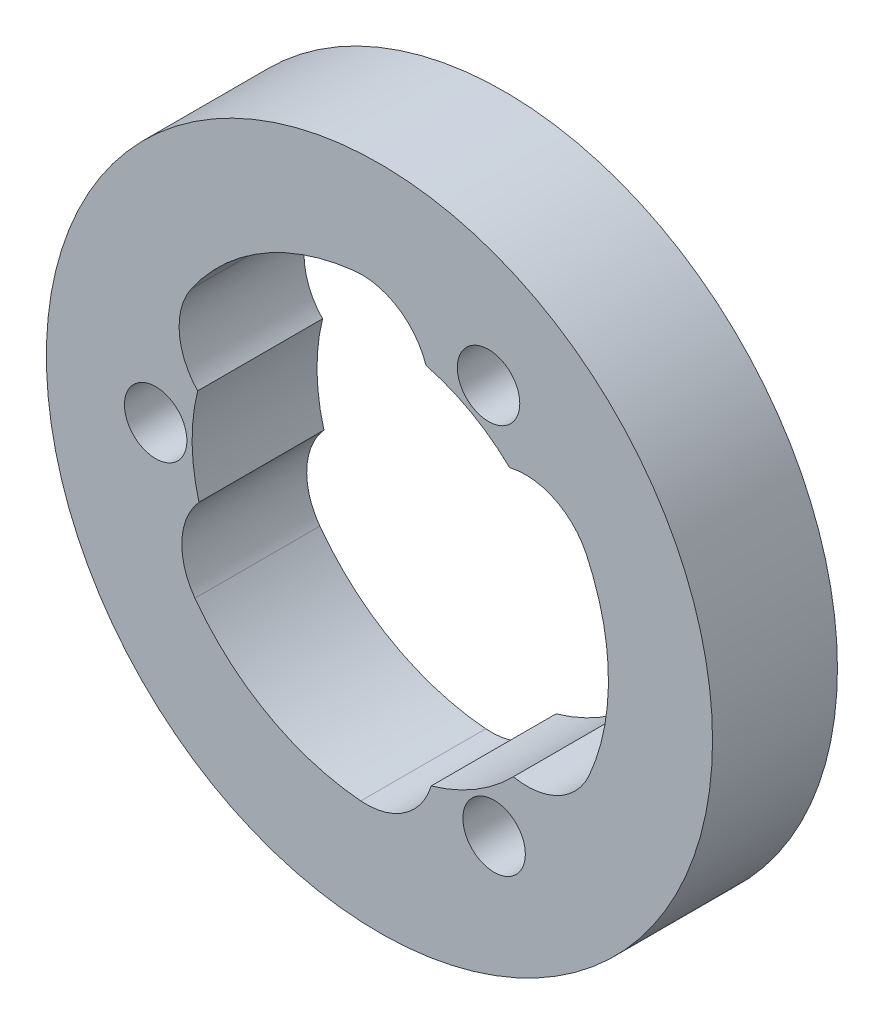
SolidWorks part; units mm, degrees
ref_plane "Plan de face" through (0, 0, 0) normal (0, 0, 1) x (1, 0, 0)
ref_plane "Plan de dessus" through (0, 0, 0) normal (0, 1, 0) x (1, 0, 0)
ref_plane "Plan de droite" through (0, 0, 0) normal (1, 0, 0) x (0, 0, -1)
sketch "Esquisse1" plane through (0, 0, 0) normal (0, 0, 1) x (1, 0, 0)
  line L0 (5.2405, 9.3862) -> (0, 0) construction
  line L1 (-10.7489, -0.1547) -> (5.2405, 9.3862) construction
  line L2 (5.2405, 9.3862) -> (5.5084, -9.2314) construction
  line L3 (5.5084, -9.2314) -> (-10.7489, -0.1547) construction
  circle A0 centre (0, 0) radius 16
  circle A3 centre (-10.7489, -0.1547) radius 1.5
  arc A4 (-8.6673, -2.4245) -> (-8.8628, -6.5154) centre (-6.2442, -4.5904) ccw
  arc A5 (-9.0466, 6.2577) -> (-8.7335, 2.174) centre (-6.3738, 4.4088) ccw
  arc A6 (-8.8628, -6.5154) -> (-0.896, -10.9635) centre (0, 0) ccw
  arc A7 (-8.686, 2.3566) -> (-8.6146, -2.6057) centre (-10.7489, -0.1547) ccw construction
  arc A8 (6.3839, 6.344) -> (2.0507, 8.7633) centre (5.2405, 9.3862) ccw construction
  circle A9 centre (5.2405, 9.3862) radius 1.5
  arc A10 (9.9426, 4.7058) -> (6.2495, 6.4764) centre (7.005, 3.3154) ccw
  arc A12 (2.234, 8.7183) -> (-1.2111, 10.9331) centre (-0.8533, 7.7029) ccw
  arc A13 (2.3021, -8.7006) -> (6.5638, -6.1576) centre (5.5084, -9.2314) ccw construction
  circle A14 centre (5.5084, -9.2314) radius 1.5
  arc A15 (-0.896, -10.9635) -> (2.484, -8.6504) centre (-0.6312, -7.7242) ccw
  arc A17 (6.4333, -6.2939) -> (10.0739, -4.4177) centre (7.0975, -3.1125) ccw
  arc A18 (10.0739, -4.4177) -> (9.9426, 4.7058) centre (0, 0) ccw
  circle A19 centre (0, 0) radius 7.75 construction
  arc A20 (-1.2111, 10.9331) -> (-9.0466, 6.2577) centre (0, 0) ccw
  arc A21 (2.484, -8.6504) -> (6.4333, -6.2939) centre (0, 0) ccw
  arc A23 (6.2495, 6.4764) -> (2.234, 8.7183) centre (0, 0) ccw
  arc A24 (-8.7335, 2.174) -> (-8.6673, -2.4245) centre (0, 0) ccw
  point P32 (0, 0)
  dimension "D1" = 32
  dimension "D2" = 6.5
  dimension "D3" = 3
  dimension "D4" = 3
  dimension "D5" = 15.5
  dimension "D7" = 18
  dimension "D9" = 11
  dimension "D10" = 3.25
  dimension "D11" = 3.25
  dimension "D12" = 7.75
  dimension "D14" = 11
  dimension "D6" = 10.75
  dimension "D13" = 7.75
extrude "Boss.-Extru.1" add sketch "Esquisse1" along normal blind 6
